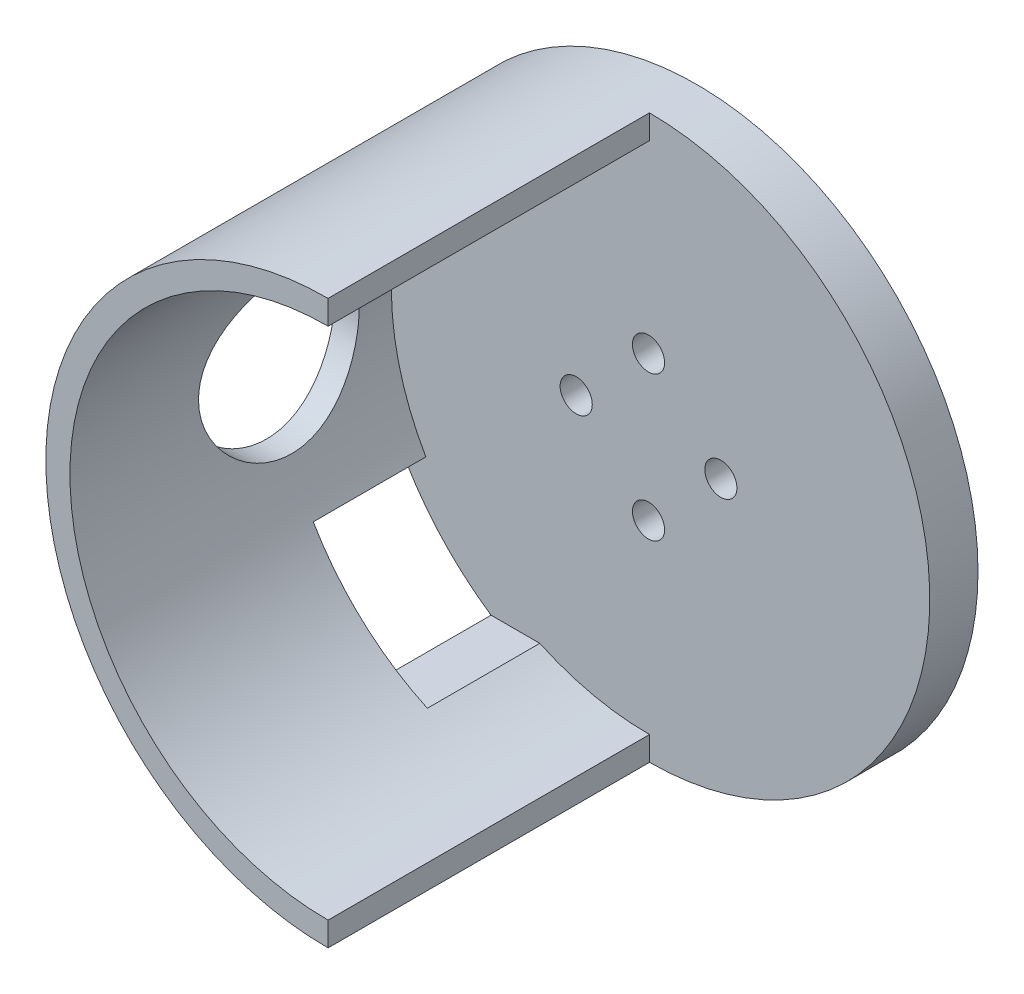
SolidWorks part; units mm, degrees
ref_plane "Ebene vorne" through (0, 0, 0) normal (0, 0, 1) x (1, 0, 0)
ref_plane "Ebene oben" through (0, 0, 0) normal (0, 1, 0) x (1, 0, 0)
ref_plane "Ebene rechts" through (0, 0, 0) normal (1, 0, 0) x (0, 0, -1)
sketch "Skizze3" plane through (0, 0, 0) normal (0, 0, 1) x (1, 0, 0)
  circle A0 centre (0, 0) radius 16
  circle A1 centre (0, 0) radius 17.5
  point P0 (0, 0)
  dimension "D1" = 32
  dimension "D2" = 35
extrude "Aufsatz-Linear austragen3" add sketch "Skizze3" along normal blind 20
sketch "Skizze4" plane through (0, 0, 0) normal (0, 0, 1) x (1, 0, 0)
  circle A0 centre (0, 0) radius 17.5
  point P0 (0, 0)
extrude "Aufsatz-Linear austragen4" add sketch "Skizze4" against normal blind 3
sketch "Skizze5" plane through (0, 0, 0) normal (1, 0, 0) x (0, 0, -1)
  line L0 (3, 0) -> (-20, 0) construction
  line L1 (-20, 17.5) -> (-20, -17.5) construction
  line L2 (3, -17.5) -> (3, 17.5) construction
  circle A0 centre (-7, 0) radius 5
  point P6 (-14.688, 10.8829)
  point P11 (3, 0)
  point P12 (-8.5695, 0)
  dimension "D1" = 10
  dimension "D2" = 10
extrude "Schnitt-Linear austragen1" cut sketch "Skizze5" against normal blind 40
sketch "Skizze6" plane through (0, 0, -3) normal (0, 0, -1) x (-1, 0, 0)
  line L0 (-21.0977, 0) -> (21.9999, 0) construction
  line L1 (0, 19.5486) -> (0, -22.0756) construction
  line L2 (0, 21.0977) -> (0, -21.9999) construction
  line L3 (21.0977, 0) -> (-21.9999, 0) construction
  line L4 (0, -21.0977) -> (0, 21.9999) construction
  circle A1 centre (-4.5, 0) radius 1
  circle A2 centre (0, 4.5) radius 1
  circle A3 centre (4.5, 0) radius 1
  circle A4 centre (0, -4.5) radius 1
  point P0 (0, 0)
  point P6 (-3.5, 0)
  point P7 (-4.5, 0)
  point P25 (0, 0)
  dimension "D1" = 3.5
  dimension "D2" = 1
  dimension "D3" = 4
extrude "Schnitt-Linear austragen2" cut sketch "Skizze6" against normal blind 10
sketch "Skizze7" plane through (0, 0, 0) normal (0, 0, 1) x (1, 0, 0)
  line L0 (0, 0) -> (16, 0) construction
  line L1 (0, 0) -> (0, 16) construction
  line L2 (0, 0) -> (0, -16) construction
  line L4 (31.9387, -17.4999) -> (0.0613, -17.4999)
  line L5 (31.9387, -17.4999) -> (31.9387, 17.4999)
  line L6 (31.9387, 17.4999) -> (0.0613, 17.4999)
  line L7 (0.0613, -17.4999) -> (0.0613, 17.4999)
  line L8 (31.9387, -17.4999) -> (0.0613, 17.4999) construction
  line L9 (31.9387, 17.4999) -> (0.0613, -17.4999) construction
  circle A0 centre (0, 0) radius 16 construction
  circle A1 centre (0, 0) radius 16 construction
  circle A2 centre (0, 0) radius 17.5 construction
  point P0 (0, 0)
  point P11 (0.0613, 17.4999)
  point P16 (0, 0)
  point P19 (0, -16)
extrude "Schnitt-Linear austragen3" cut sketch "Skizze7" along normal blind 30
sketch "Skizze8" plane through (0, 0, 0) normal (1, 0, 0) x (0, 0, -1)
  line L0 (3, -17.5) -> (3, 17.5) construction
  line L1 (-7, -5) -> (-7, -17.5) construction
  line L2 (-20, -17.5) -> (3, -17.5) construction
  line L3 (-7, -5) -> (3, -5) construction
  line L4 (0, 17.4999) -> (0, -17.4999) construction
  line L5 (0, -8) -> (-7, -8)
  line L6 (0, -8) -> (0, -14.5)
  line L7 (0, -14.5) -> (-7, -14.5)
  line L8 (-7, -8) -> (-7, -14.5)
  circle A0 centre (-7, 0) radius 5 construction
  point P0 (3, -17.4896)
  point P1 (-7, -5)
  point P4 (-2, 0)
  point P7 (3, 0)
  point P17 (-3.5, -14.5)
  dimension "D1" = 3
  dimension "D2" = 0
  dimension "D3" = 3
  dimension "D4" = 7
extrude "Schnitt-Linear austragen4" cut sketch "Skizze8" against normal blind 30
